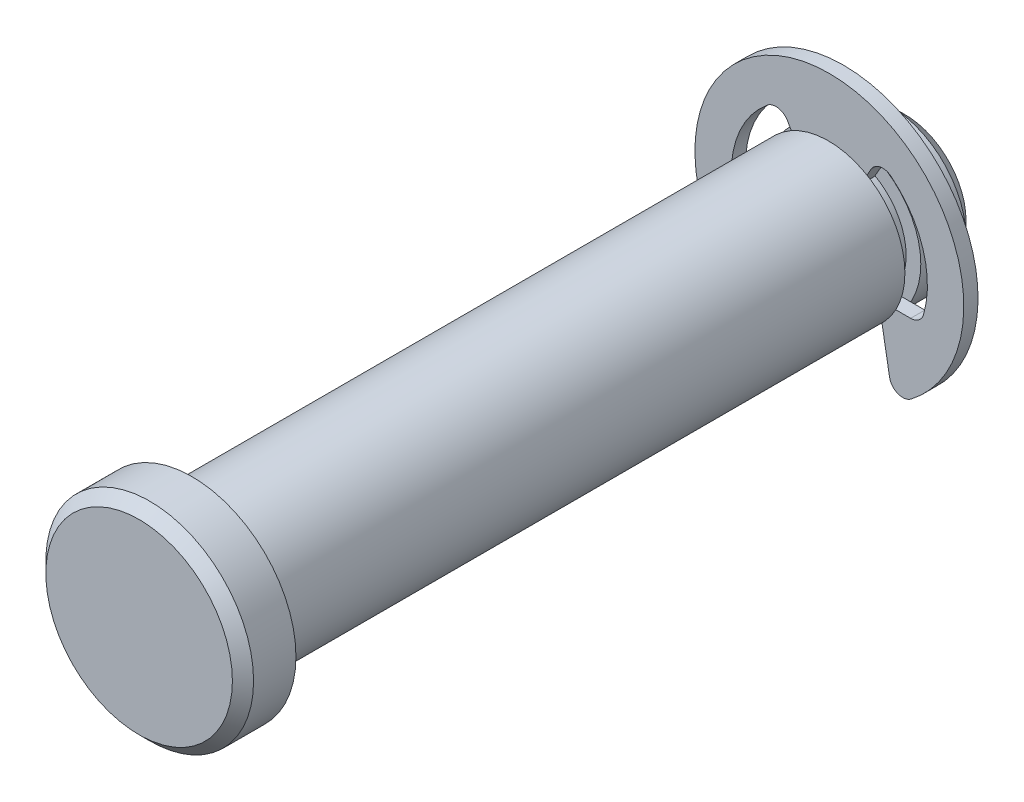
SolidWorks part; units mm, degrees
ref_plane "Front" through (0, 0, 0) normal (0, 0, 1) x (1, 0, 0)
ref_plane "Top" through (0, 0, 0) normal (0, 1, 0) x (1, 0, 0)
ref_plane "Right" through (0, 0, 0) normal (1, 0, 0) x (0, 0, -1)
sketch "Sketch2" plane through (0, 0, 0) normal (0, 0, 1) x (1, 0, 0)
  circle A0 centre (0, 0) radius 4.7625
  point P3 (0, 4.7625)
  point P4 (0, -4.7625)
  dimension "dia" = 9.525
extrude "Extrude1" add sketch "Sketch2" along normal mid plane 44.45
sketch "Sketch3" plane through (0, 0, 0) normal (1, 0, 0) x (0, 0, -1)
  line L0 (22.225, 4.7625) -> (-22.225, 4.7625) construction
  line L1 (17.4625, 4.7625) -> (18.4531, 4.7625)
  line L2 (17.4625, 4.7625) -> (17.4625, 3.8481)
  line L3 (17.4625, 3.8481) -> (18.4531, 3.8481)
  line L4 (18.4531, 4.7625) -> (18.4531, 3.8481)
  line L5 (-22.225, 4.7625) -> (-22.225, -4.7625) construction
  line L10 (18.4531, 3.8481) -> (18.4531, -3.8481) construction
  point P11 (18.4531, 0)
  point P14 (17.9578, 4.7625)
  dimension "groove wd" = 0.9906
  dimension "groove dia" = 7.6962
  dimension "usable lg" = 39.6875
revolve "Cut-Revolve1" cut sketch "Sketch3" angle 360 about axis through (0, 0, 22.225) along (0, 0, -1)
sketch "Sketch8" plane through (0, 0, 22.225) normal (0, 0, 1) x (1, 0, 0)
  circle A0 centre (0, 0) radius 6.477
  dimension "head dia" = 12.954
extrude "Extrude6" add sketch "Sketch8" along normal blind 3.302
chamfer "Chamfer2" distance 0.6604 angle 45 1 edges at (6.477, 0, 25.527)
ref_plane "Plane1" through (0, 0, -17.9578) normal (0, 0, 1) x (1, 0, 0)
sketch "Sketch4" plane through (0, 0, -17.9578) normal (0, 0, 1) x (1, 0, 0)
  line L0 (0, 3.8481) -> (0, -3.8481) construction
  circle A0 centre (0, 0) radius 8.382
  circle A1 centre (0, 0) radius 3.8481
  dimension "ring dia" = 16.764
extrude "Extrude2" add sketch "Sketch4" along normal mid plane 0.889 separate body
sketch "Sketch5" plane through (0, 0, 0) normal (0, 0, 1) x (1, 0, 0)
  line L0 (0, 8.382) -> (0, 3.8481) construction
  line L1 (-3.0575, 5.2958) -> (0, 0)
  line L2 (-5.6624, -2.3089) -> (-3.0785, -2.3089)
  line L3 (0, 0) -> (3.0575, 5.2958)
  line L4 (-3.0785, -2.3089) -> (-3.9728, -7.3807)
  line L5 (3.0785, -2.3089) -> (3.9728, -7.3807)
  line L6 (3.0785, -2.3089) -> (5.6624, -2.3089)
  arc A0 (-3.0575, 5.2958) -> (-5.6624, -2.3089) centre (0, 0) ccw
  circle A1 centre (0, 0) radius 8.382 construction
  circle A2 centre (0, 0) radius 3.8481 construction
  arc A3 (5.6624, -2.3089) -> (3.0575, 5.2958) centre (0, 0) ccw
  arc A4 (-3.9728, -7.3807) -> (3.9728, -7.3807) centre (0, 0) ccw
  circle A5 centre (0, 0) radius 3.8481 construction
  point P10 (0, 6.1151)
  dimension "D1" = 30
  dimension "D2" = 10
  dimension "D3" = 2.3089
extrude "Extrude4" cut sketch "Sketch5" against normal through all
sketch "Sketch6" plane through (0, 0, -17.5133) normal (0, 0, 1) x (1, 0, 0)
  line L0 (-1.9241, 3.3326) -> (1.9241, 3.3326)
  circle A0 centre (0, 0) radius 3.8481 construction
  arc A1 (1.9241, 3.3326) -> (-1.9241, 3.3326) centre (0, 0) ccw
extrude "Extrude5" add sketch "Sketch6" against normal up to surface (0.889 mm away) up to face at (0, 1.0514, -18.4023)
fillet "Fillet1" radius 0.8382 6 edges at (3.9728, -7.3807, -17.9578) (-3.9728, -7.3807, -17.9578) (5.6624, -2.3089, -17.9578) (3.0575, 5.2958, -17.9578) (-3.0575, 5.2958, -17.9578) (-5.6624, -2.3089, -17.9578)
chamfer "Chamfer1" distance 0.9525 angle 45 1 edges at (4.7625, 0, -22.225)
sketch "Sketch7" plane through (0, 0, 0) normal (1, 0, 0) x (0, 0, -1)
  line L0 (18.4023, 8.382) -> (17.5133, 8.382) construction
  line L1 (22.225, -4.7625) -> (22.225, 4.7625) construction
  line L2 (17.5133, -6.8329) -> (18.4023, -6.8329) construction
  line L3 (-25.527, 5.8166) -> (-25.527, -5.8166) construction
  point P0 (18.4531, -6.8329)
  point P1 (22.225, 4.7625)
  point P2 (-25.527, 6.477)
  point P6 (17.4625, 8.382)
  point P7 (22.225, -4.7625)
  point P12 (-22.225, 6.477)
  point P16 (17.4625, -6.8329)
equation "\"D1@Chamfer1\" = \"dia@Sketch2\" * .1"
equation "\"D1@Fillet1\" = \"ring dia@Sketch4\" * .05"
equation "\"D3@Sketch5\" = \"groove dia@Sketch3\" * .3"
equation "\"D1@Chamfer2\" = \"head ht@Extrude6\" * .2"
